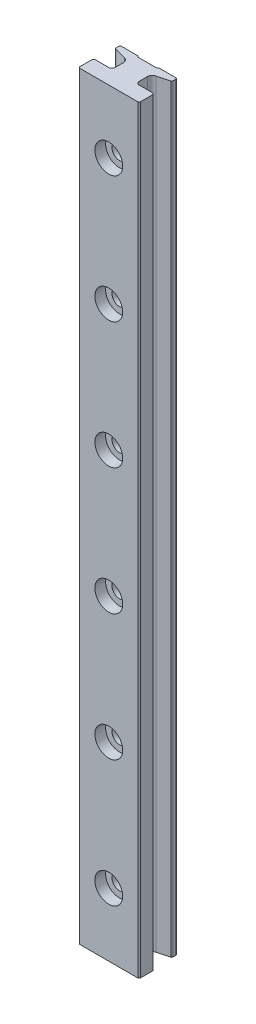
SolidWorks part; units mm, degrees
ref_plane "Front Plane" through (0, 0, 0) normal (0, 0, 1) x (1, 0, 0)
ref_plane "Top Plane" through (0, 0, 0) normal (0, 1, 0) x (1, 0, 0)
ref_plane "Right Plane" through (0, 0, 0) normal (1, 0, 0) x (0, 0, -1)
ref_plane "Plane1" through (0, 0, 6.3) normal (0, 0, 1) x (1, 0, 0)
sketch "Sketch1" plane through (0, 0, 6.3) normal (0, 0, 1) x (1, 0, 0)
  line L0 (4.5, 60) -> (-4.5, 60)
  line L1 (-4.5, 60) -> (-4.5, -60)
  line L2 (-4.5, -60) -> (4.5, -60)
  line L3 (4.5, -60) -> (4.5, 60)
extrude "Boss-Extrude1" add sketch "Sketch1" against normal blind 6.3
sketch "Sketch2" plane through (0, 60, 0) normal (0, 1, 0) x (-1, 0, 0)
  line L0 (4.5, 6.3) -> (1.9, 6.3)
  line L1 (1.9, 6.3) -> (1.9, 1.4967)
  line L2 (1.9, 1.4967) -> (4.5, 0.8)
  line L3 (4.5, 0.8) -> (4.5, 6.3)
extrude "Cut-Extrude1" cut sketch "Sketch2" against normal through all
sketch "Sketch3" plane through (-1.9, 0, 0) normal (-1, 0, 0) x (0, 0, 1)
  line L0 (6.3, -60) -> (3.9, -60)
  line L1 (3.9, -60) -> (3.9, 60)
  line L2 (3.9, 60) -> (6.3, 60)
  line L3 (6.3, 60) -> (6.3, -60)
extrude "Boss-Extrude2" add sketch "Sketch3" along normal blind 2.9
sketch "Sketch4" plane through (0, 60, 0) normal (0, 1, 0) x (-1, 0, 0)
  line L0 (-4.5, 0.8) -> (-1.9, 1.4967)
  line L1 (-1.9, 1.4967) -> (-1.9, 6.3)
  line L2 (-1.9, 6.3) -> (-4.5, 6.3)
  line L3 (-4.5, 6.3) -> (-4.5, 0.8)
extrude "Cut-Extrude2" cut sketch "Sketch4" against normal through all
sketch "Sketch5" plane through (1.9, 0, 0) normal (1, 0, 0) x (0, 0, -1)
  line L0 (-3.9, -60) -> (-6.3, -60)
  line L1 (-6.3, -60) -> (-6.3, 60)
  line L2 (-6.3, 60) -> (-3.9, 60)
  line L3 (-3.9, 60) -> (-3.9, -60)
extrude "Boss-Extrude3" add sketch "Sketch5" along normal blind 2.9
sketch "Sketch6" plane through (0, -60, 0) normal (0, -1, 0) x (1, 0, 0)
  line L0 (-1.7, 0) -> (1.7, 0)
  line L1 (1.7, 0) -> (1.52, 0.18)
  line L2 (1.52, 0.18) -> (-1.52, 0.18)
  line L3 (-1.52, 0.18) -> (-1.7, 0)
extrude "Cut-Extrude3" cut sketch "Sketch6" against normal through all
hole_wizard "Hole1" positions "Sketch8" profile "Sketch7" legacy
sketch "Sketch8" plane through (0, 0, 6.3) normal (0, 0, 1) x (1, 0, 0)
  point P0 (0, -50)
sketch "Sketch7" plane through (0, -50, 6.3) normal (1, 0, 0) x (0, -1, 0)
  line L0 (0, 0) -> (0, 6.3)
  line L1 (0, 6.3) -> (1.2, 6.3)
  line L2 (1.2, 6.3) -> (1.2, 1.7)
  line L3 (1.2, 1.7) -> (2.2, 1.7)
  line L4 (2.2, 1.7) -> (2.2, 0)
  line L5 (2.2, 0) -> (0, 0)
  line L6 (0, 110) -> (0, -10) construction
  dimension "Diameter" = 2.4
  dimension "Depth" = 6.3
  dimension "C-Bore Diameter" = 4.4
  dimension "C-Bore Depth" = 1.7
hole_wizard "Hole2" positions "Sketch10" profile "Sketch9" legacy
sketch "Sketch10" plane through (0, 0, 6.3) normal (0, 0, 1) x (1, 0, 0)
  point P0 (0, -30)
sketch "Sketch9" plane through (0, -30, 6.3) normal (1, 0, 0) x (0, -1, 0)
  line L0 (0, 0) -> (0, 6.3)
  line L1 (0, 6.3) -> (1.2, 6.3)
  line L2 (1.2, 6.3) -> (1.2, 1.7)
  line L3 (1.2, 1.7) -> (2.2, 1.7)
  line L4 (2.2, 1.7) -> (2.2, 0)
  line L5 (2.2, 0) -> (0, 0)
  line L6 (0, 110) -> (0, -10) construction
  dimension "Diameter" = 2.4
  dimension "Depth" = 6.3
  dimension "C-Bore Diameter" = 4.4
  dimension "C-Bore Depth" = 1.7
hole_wizard "Hole3" positions "Sketch12" profile "Sketch11" legacy
sketch "Sketch12" plane through (0, 0, 6.3) normal (0, 0, 1) x (1, 0, 0)
  point P0 (0, -10)
sketch "Sketch11" plane through (0, -10, 6.3) normal (1, 0, 0) x (0, -1, 0)
  line L0 (0, 0) -> (0, 6.3)
  line L1 (0, 6.3) -> (1.2, 6.3)
  line L2 (1.2, 6.3) -> (1.2, 1.7)
  line L3 (1.2, 1.7) -> (2.2, 1.7)
  line L4 (2.2, 1.7) -> (2.2, 0)
  line L5 (2.2, 0) -> (0, 0)
  line L6 (0, 110) -> (0, -10) construction
  dimension "Diameter" = 2.4
  dimension "Depth" = 6.3
  dimension "C-Bore Diameter" = 4.4
  dimension "C-Bore Depth" = 1.7
hole_wizard "Hole4" positions "Sketch14" profile "Sketch13" legacy
sketch "Sketch14" plane through (0, 0, 6.3) normal (0, 0, 1) x (1, 0, 0)
  point P0 (0, 10)
sketch "Sketch13" plane through (0, 10, 6.3) normal (1, 0, 0) x (0, -1, 0)
  line L0 (0, 0) -> (0, 6.3)
  line L1 (0, 6.3) -> (1.2, 6.3)
  line L2 (1.2, 6.3) -> (1.2, 1.7)
  line L3 (1.2, 1.7) -> (2.2, 1.7)
  line L4 (2.2, 1.7) -> (2.2, 0)
  line L5 (2.2, 0) -> (0, 0)
  line L6 (0, 110) -> (0, -10) construction
  dimension "Diameter" = 2.4
  dimension "Depth" = 6.3
  dimension "C-Bore Diameter" = 4.4
  dimension "C-Bore Depth" = 1.7
hole_wizard "Hole5" positions "Sketch16" profile "Sketch15" legacy
sketch "Sketch16" plane through (0, 0, 6.3) normal (0, 0, 1) x (1, 0, 0)
  point P0 (0, 30)
sketch "Sketch15" plane through (0, 30, 6.3) normal (1, 0, 0) x (0, -1, 0)
  line L0 (0, 0) -> (0, 6.3)
  line L1 (0, 6.3) -> (1.2, 6.3)
  line L2 (1.2, 6.3) -> (1.2, 1.7)
  line L3 (1.2, 1.7) -> (2.2, 1.7)
  line L4 (2.2, 1.7) -> (2.2, 0)
  line L5 (2.2, 0) -> (0, 0)
  line L6 (0, 110) -> (0, -10) construction
  dimension "Diameter" = 2.4
  dimension "Depth" = 6.3
  dimension "C-Bore Diameter" = 4.4
  dimension "C-Bore Depth" = 1.7
hole_wizard "Hole6" positions "Sketch18" profile "Sketch17" legacy
sketch "Sketch18" plane through (0, 0, 6.3) normal (0, 0, 1) x (1, 0, 0)
  point P0 (0, 50)
sketch "Sketch17" plane through (0, 50, 6.3) normal (1, 0, 0) x (0, -1, 0)
  line L0 (0, 0) -> (0, 6.3)
  line L1 (0, 6.3) -> (1.2, 6.3)
  line L2 (1.2, 6.3) -> (1.2, 1.7)
  line L3 (1.2, 1.7) -> (2.2, 1.7)
  line L4 (2.2, 1.7) -> (2.2, 0)
  line L5 (2.2, 0) -> (0, 0)
  line L6 (0, 110) -> (0, -10) construction
  dimension "Diameter" = 2.4
  dimension "Depth" = 6.3
  dimension "C-Bore Diameter" = 4.4
  dimension "C-Bore Depth" = 1.7
chamfer "Chamfer1" distance 0.2 angle 45 1 edges at (4.8, 0, 6.3)
chamfer "Chamfer2" distance 0.3 angle 45 1 edges at (1.9, 0, 3.9)
chamfer "Chamfer3" distance 0.2 angle 45 1 edges at (-4.8, 0, 6.3)
chamfer "Chamfer4" distance 0.3 angle 45 1 edges at (-1.9, 0, 3.9)
chamfer "Chamfer5" distance 0.2 angle 45 1 edges at (-4.8, 0, 3.9)
chamfer "Chamfer6" distance 0.2 angle 45 1 edges at (4.8, 0, 3.9)
fillet "Fillet1" radius 0.2 1 edges at (-4.5, 0, 0)
fillet "Fillet2" radius 0.2 1 edges at (-4.5, 0, 0.8)
fillet "Fillet3" radius 0.2 1 edges at (4.5, 0, 0)
fillet "Fillet4" radius 0.2 1 edges at (4.5, 0, 0.8)
fillet "Fillet5" radius 0.8 1 edges at (-1.9, 0, 1.4967)
fillet "Fillet6" radius 0.8 1 edges at (1.9, 0, 1.4967)
